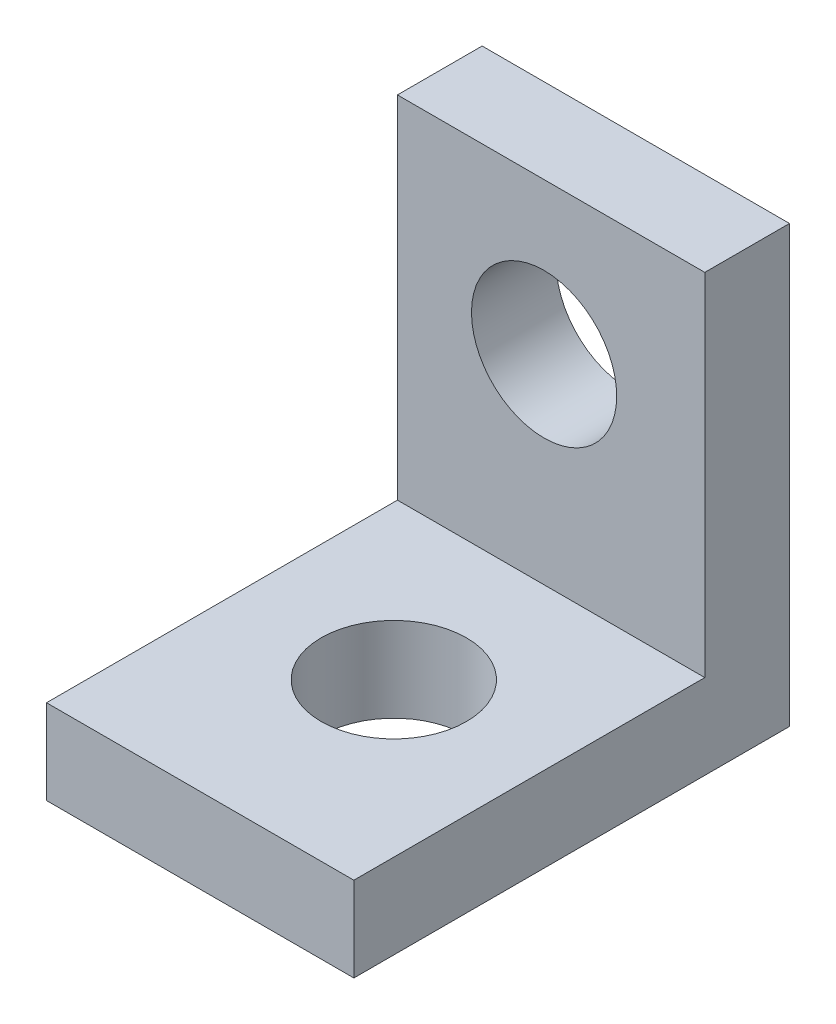
SolidWorks part; units mm, degrees
ref_plane "Front Plane" through (0, 0, 0) normal (0, 0, 1) x (1, 0, 0)
ref_plane "Top Plane" through (0, 0, 0) normal (0, 1, 0) x (1, 0, 0)
ref_plane "Right Plane" through (0, 0, 0) normal (1, 0, 0) x (0, 0, -1)
sketch "Sketch1" plane through (0, 0, 0) normal (0, 1, 0) x (1, 0, 0)
  line L1 (-0.6048, 2.0411) -> (5.7452, 2.0411)
  line L2 (-0.6048, 2.0411) -> (-0.6048, -6.9589)
  line L3 (-0.6048, -6.9589) -> (5.7452, -6.9589)
  line L4 (5.7452, 2.0411) -> (5.7452, -6.9589)
  circle A0 centre (2.5702, -2.9589) radius 1.5
  dimension "D3" = 3
  dimension "D1" = 9
  dimension "D2" = 6.35
  dimension "D4" = 4
  dimension "3.45" = 3.175
extrude "Boss-Extrude1" add sketch "Sketch1" along normal blind 1.75
sketch "Sketch2" plane through (0, 1.75, 0) normal (0, 1, 0) x (1, 0, 0)
  line L0 (5.7452, -6.9589) -> (5.7452, 2.0411) construction
  line L1 (-0.6048, 2.0411) -> (5.7452, 2.0411)
  line L2 (-0.6048, 2.0411) -> (-0.6048, 0.2911)
  line L3 (-0.6048, 0.2911) -> (5.7452, 0.2911)
  line L4 (5.7452, 2.0411) -> (5.7452, 0.2911)
  dimension "D1" = 1.75
extrude "Boss-Extrude2" add sketch "Sketch2" along normal blind 7.25
sketch "Sketch3" plane through (0, 0, -0.2911) normal (0, 0, 1) x (1, 0, 0)
  line L2 (-0.6048, 9) -> (5.7452, 9) construction
  line L3 (5.7452, 9) -> (5.7452, 1.75) construction
  circle A0 centre (2.4252, 5.875) radius 1.5
  dimension "D1" = 3
  dimension "D3" = 3.125
  dimension "D2" = 3.32
extrude "Cut-Extrude1" cut sketch "Sketch3" against normal through all both and the other way through all
